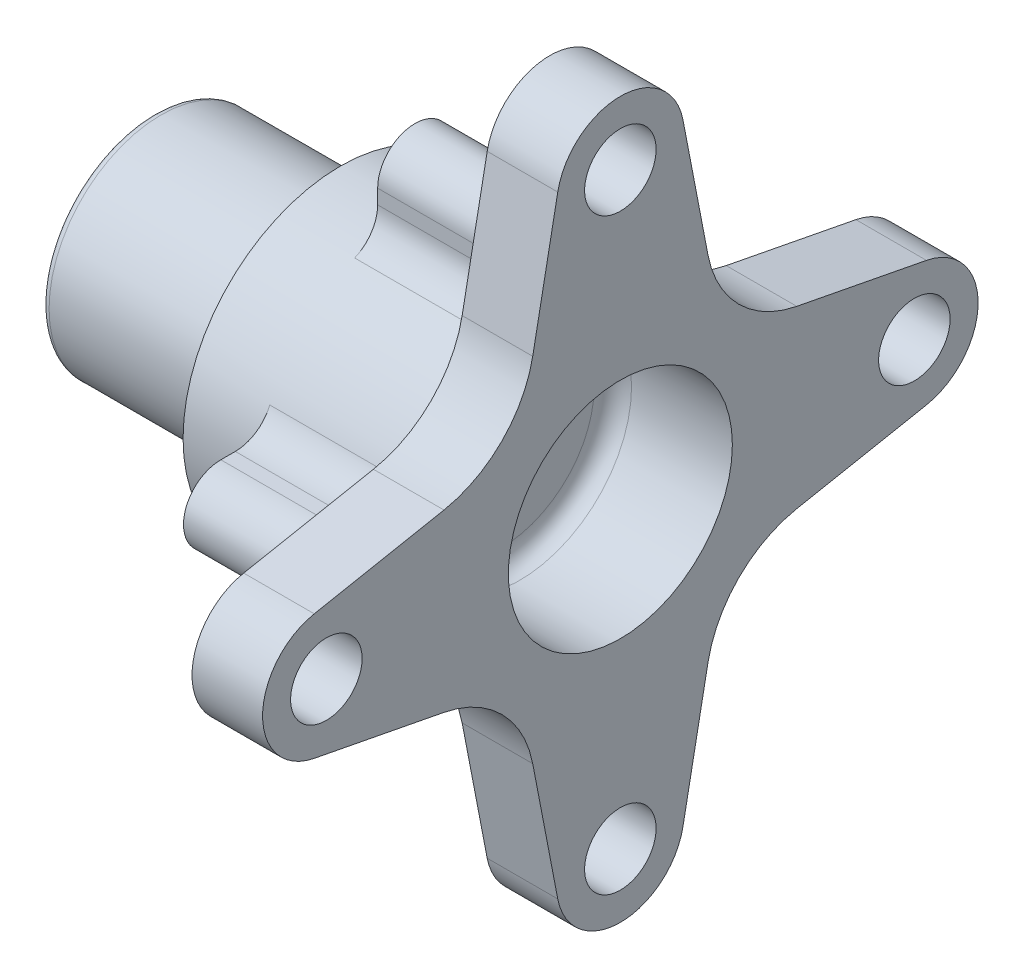
SolidWorks part; units mm, degrees
material "Plain Carbon Steel"
ref_plane "Front" through (0, 0, 0) normal (0, 0, 1) x (1, 0, 0)
ref_plane "Top" through (0, 0, 0) normal (0, 1, 0) x (1, 0, 0)
ref_plane "Right" through (0, 0, 0) normal (1, 0, 0) x (0, 0, -1)
sketch "Sketch1" plane through (0, 0, 0) normal (0, 0, 1) x (1, 0, 0)
  line L0 (479.9414, 251.46) -> (511.6914, 251.46)
  line L1 (524.3914, 259.155) -> (524.3914, 271.78)
  line L2 (511.6914, 251.46) -> (511.6914, 259.155)
  line L3 (511.6914, 259.155) -> (524.3914, 259.155)
  line L4 (470.4164, 259.155) -> (470.4164, 205.665) construction
  line L5 (524.3914, 271.78) -> (547.3164, 271.78)
  line L6 (479.9414, 251.46) -> (479.9414, 238.76)
  line L7 (439.5414, 232.41) -> (559.3164, 232.41) construction
  line L8 (547.3164, 271.78) -> (547.3164, 293.5225)
  line L9 (547.3164, 293.5225) -> (559.3164, 293.5225)
  line L10 (559.3164, 293.5225) -> (559.3164, 238.76)
  line L12 (559.3164, 238.76) -> (479.9414, 238.76)
  line L14 (511.6914, 205.665) -> (511.6914, 259.155) construction
  line L15 (511.6914, 205.665) -> (511.6914, 259.155) construction
  line L17 (559.3164, 303.1332) -> (559.3164, 182.4012) construction
  dimension "D1" = 61.1125
  dimension "D3" = 12
  dimension "D5" = 19.05
  dimension "D2" = 6.35
  dimension "D9" = 12.7
  dimension "D4" = 39.37
  dimension "D6" = 12.7
  dimension "D7" = 9.525
revolve "Revolve1" add sketch "Sketch1" angle 360 about L7
sketch "Sketch2" plane through (559.3164, 0, 0) normal (1, 0, 0) x (0, 0, -1)
  line L0 (10.6454, 284.4652) -> (14.9039, 262.4074)
  line L1 (-10.6454, 284.4652) -> (-14.9039, 262.4074)
  line L2 (52.0552, 243.0554) -> (29.9974, 247.3139)
  line L3 (52.0552, 221.7646) -> (29.9974, 217.5061)
  line L4 (10.6454, 180.3548) -> (14.9039, 202.4126)
  line L5 (-10.6454, 180.3548) -> (-14.9039, 202.4126)
  line L6 (-52.0552, 221.7646) -> (-29.9974, 217.5061)
  line L7 (-52.0552, 243.0554) -> (-29.9974, 247.3139)
  circle A0 centre (0, 282.41) radius 6.0795
  arc A1 (29.9974, 247.3139) -> (14.9039, 262.4074) centre (33.6085, 266.0185) cw
  circle A2 centre (0, 232.41) radius 26.745 construction
  circle A3 centre (50, 232.41) radius 6.0795
  circle A4 centre (0, 182.41) radius 6.0795
  circle A5 centre (-50, 232.41) radius 6.0795
  circle A6 centre (0, 282.41) radius 10.842
  circle A7 centre (-50, 232.41) radius 10.842
  circle A8 centre (0, 182.41) radius 10.842
  circle A9 centre (50, 232.41) radius 10.842
  circle A10 centre (0, 232.41) radius 20.32
  arc A11 (-29.9974, 247.3139) -> (-14.9039, 262.4074) centre (-33.6085, 266.0185) ccw
  arc A12 (14.9039, 202.4126) -> (29.9974, 217.5061) centre (33.6085, 198.8015) cw
  arc A13 (-27.6842, 216.9069) -> (-15.0935, 203.2845) centre (-33.6085, 198.8015) cw
  arc A14 (-27.6842, 216.9069) -> (-15.0935, 203.2845) centre (-33.6085, 198.8015) cw
  arc A15 (-29.9974, 217.5061) -> (-14.9039, 202.4126) centre (-33.6085, 198.8015) cw
  circle A16 centre (0, 232.41) radius 26.745 construction
  point P14 (0, 232.41)
  point P42 (0, 232.41)
  circle M2 centre (0, 232.41) radius 61.1125
  dimension "D1" = 12.159
  dimension "D5" = 40.64
  dimension "D7" = 19.05
  dimension "D8" = 19.05
  dimension "D9" = 19.05
  dimension "D2" = 50
  dimension "D4" = 4.7625
  dimension "D3" = 4
  dimension "D6" = 4
extrude "Cut-Extrude1" cut sketch "Sketch2" along direction (-1, 0, 0) on the side against the normal up to surface (12 mm away) contours A15 L6 A7 L7 A11 L1 A6 L0 A1 L2 A9 L3 A12 L4 A8 L5 A13 M2 | A5 | A4 | A3 | A0
sketch "Sketch3" plane through (479.9414, 0, 0) normal (-1, 0, 0) x (0, 0, 1)
  circle A0 centre (0, 245.11) radius 3.175
  circle A1 centre (10.9985, 238.76) radius 3.175
  circle A2 centre (10.9985, 226.06) radius 3.175
  circle A3 centre (0, 219.71) radius 3.175
  circle A4 centre (-10.9985, 226.06) radius 3.175
  circle A5 centre (-10.9985, 238.76) radius 3.175
  circle A6 centre (0, 232.41) radius 6.35 construction
  point P4 (0, 232.41)
  point P14 (0, 232.41)
  dimension "D1" = 6.35
  dimension "D2" = 12.7
  dimension "D3" = 6
hole_wizard "3/16 (0.1875) Dowel Hole1" positions "3DSketch1" profile "Sketch4" hole size "3/16" standard "ANSI Inch"
sketch3d "3DSketch1"
  point P0 (479.9414, 238.76, -10.9985)
  point P3 (479.9414, 245.11, 0)
  point P6 (479.9414, 238.76, 10.9985)
  point P9 (479.9414, 226.06, 10.9985)
  point P12 (479.9414, 219.71, 0)
  point P15 (479.9414, 226.06, -10.9985)
sketch "Sketch4" plane through (479.9414, 238.76, -10.9985) normal (0, 1, 0) x (0, 0, 1)
  line L0 (0, 0) -> (0, 14.1308)
  line L1 (0, 14.1308) -> (2.3812, 12.7)
  line L2 (2.3812, 12.7) -> (2.3812, 0)
  line L5 (2.3812, 0) -> (0, 0)
  line L10 (0, 14.1308) -> (-2.3812, 12.7) construction
  line L11 (0, -6.35) -> (0, 107.95) construction
  dimension "Hole Dia." = 4.7625
  dimension "Hole Depth" = 12.7
  dimension "Drill Angle" = 118
sketch "Sketch5" plane through (524.3914, 0, 0) normal (-1, 0, 0) x (0, 0, 1)
  line L0 (-6.35, 265.43) -> (-6.35, 258.3903)
  line L1 (6.35, 265.43) -> (6.35, 258.3903)
  line L2 (33.02, 238.76) -> (25.9803, 238.76)
  line L3 (33.02, 226.06) -> (25.9803, 226.06)
  line L4 (6.35, 199.39) -> (6.35, 206.4297)
  line L5 (-6.35, 199.39) -> (-6.35, 206.4297)
  line L6 (-33.02, 226.06) -> (-25.9803, 226.06)
  line L7 (-33.02, 238.76) -> (-25.9803, 238.76)
  arc A1 (6.35, 265.43) -> (-6.35, 265.43) centre (0, 265.43) ccw
  circle A3 centre (0, 232.41) radius 26.745 construction
  circle A4 centre (0, 232.41) radius 26.745
  arc A5 (33.02, 226.06) -> (33.02, 238.76) centre (33.02, 232.41) ccw
  arc A7 (-6.35, 199.39) -> (6.35, 199.39) centre (0, 199.39) ccw
  arc A9 (-33.02, 238.76) -> (-33.02, 226.06) centre (-33.02, 232.41) ccw
  circle A11 centre (0, 232.41) radius 39.37 construction
  point P7 (0, 232.41)
  point P38 (0, 232.41)
  circle M4 centre (0, 232.41) radius 39.37
  circle M12 centre (0, 232.41) radius 26.745
  dimension "D1" = 12.7
  dimension "D2" = 4
extrude "Cut-Extrude3" cut sketch "Sketch5" against normal up to surface (22.925 mm away) contours A9 A7 L5 L6 M4 M12 | A9 L7 L0 A1 M12 M4 | A5 A1 L1 L2 M4 M12 | A7 A5 L3 L4 M4 M12 up to face at (547.3164, 282.41, 6.0795)
sketch "Sketch6" plane through (559.3164, 0, 0) normal (1, 0, 0) x (0, 0, -1)
  circle A0 centre (0, 232.41) radius 19.05
  dimension "D1" = 38.1
extrude "Cut-Extrude4" cut sketch "Sketch6" against normal blind 20.32
fillet "Fillet8" radius 6.35 8 edges at (535.8539, 258.3903, -6.35) (535.8539, 238.76, -25.9803) (535.8539, 206.4297, -6.35) (535.8539, 206.4297, 6.35) (535.8539, 226.06, 25.9803) (535.8539, 238.76, 25.9803) (535.8539, 258.3903, 6.35) (535.8539, 226.06, -25.9803)
fillet "Fillet7" radius 1.27 2 edges at (479.9414, 232.41, 6.35) (479.9414, 232.41, 19.05)
fillet "Fillet9" radius 3.175 1 edges at (538.9964, 232.41, -19.05)
hole_wizard "1/4-20 Tapped Hole1" positions "3DSketch2" profile "Sketch7" tap size "1/4-20" standard "ANSI Inch"
sketch3d "3DSketch2"
  circle A4 centre (524.3914, 232.41, 0) radius 34.29
  circle A5 centre (481.2114, 232.41, 0) radius 6.35 construction
  point P0 (524.3914, 232.41, -34.29)
  point P2 (524.3914, 266.7, 0)
  point P4 (524.3914, 232.41, 34.29)
  point P6 (524.3914, 198.12, 0)
  point P33 (558.6814, 232.41, 0)
  point P38 (474.8614, 232.41, 0)
  dimension "D1" = 34.29
cosmetic thread "Hole Thread1" parameters "D1"=12.7, "D2"=6.35
cosmetic thread "Hole Thread2" parameters "D1"=12.7, "D2"=6.35
cosmetic thread "Hole Thread3" parameters "D1"=12.7, "D2"=6.35
cosmetic thread "Hole Thread4" parameters "D1"=12.7, "D2"=6.35
sketch "Sketch7" plane through (524.3914, 232.41, -34.29) normal (0, 1, 0) x (0, 0, 1)
  line L0 (0, 0) -> (0, 18.0438)
  line L1 (0, 18.0438) -> (2.5527, 16.51)
  line L2 (2.5527, 16.51) -> (2.5527, 0)
  line L5 (2.5527, 0) -> (0, 0)
  line L10 (0, 18.0438) -> (-2.5527, 16.51) construction
  line L11 (0, -6.35) -> (0, 107.95) construction
  dimension "Tap Drill Dia." = 5.1054
  dimension "Tap Drill Depth" = 16.51
  dimension "Drill Angle" = 118
equation "\"D1@Sketch1\"=50mm+.375+.0625"
equation "\"D1@Sketch2\"=.4787"
equation "\"D2@Sketch2\"=50mm"
